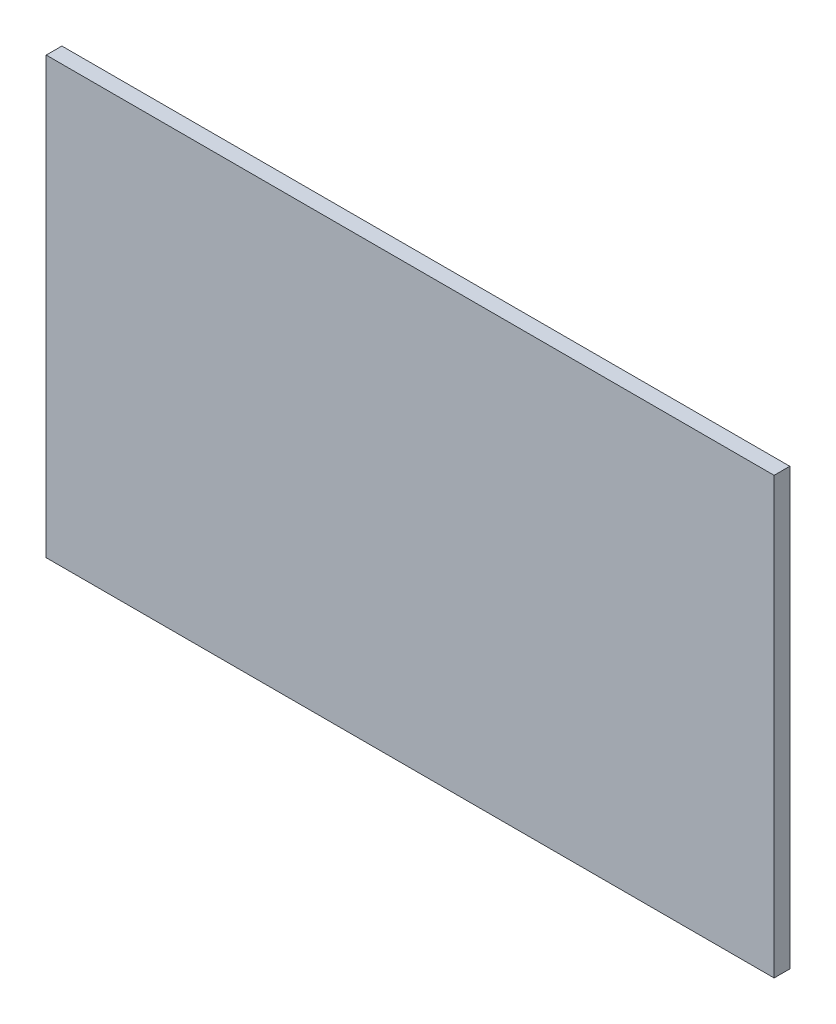
SolidWorks part; units mm, degrees
ref_plane "Front Plane" through (0, 0, 0) normal (0, 0, 1) x (1, 0, 0)
ref_plane "Top Plane" through (0, 0, 0) normal (0, 1, 0) x (1, 0, 0)
ref_plane "Right Plane" through (0, 0, 0) normal (1, 0, 0) x (0, 0, -1)
sketch "Sketch1" plane through (0, 0, 0) normal (0, 0, 1) x (1, 0, 0)
  line L1 (0, 0) -> (418, 0)
  line L2 (0, 0) -> (0, 250)
  line L3 (0, 250) -> (418, 250)
  line L4 (418, 0) -> (418, 250)
  dimension "D1" = 418
  dimension "D2" = 250
extrude "Boss-Extrude1" add sketch "Sketch1" along normal blind 9
